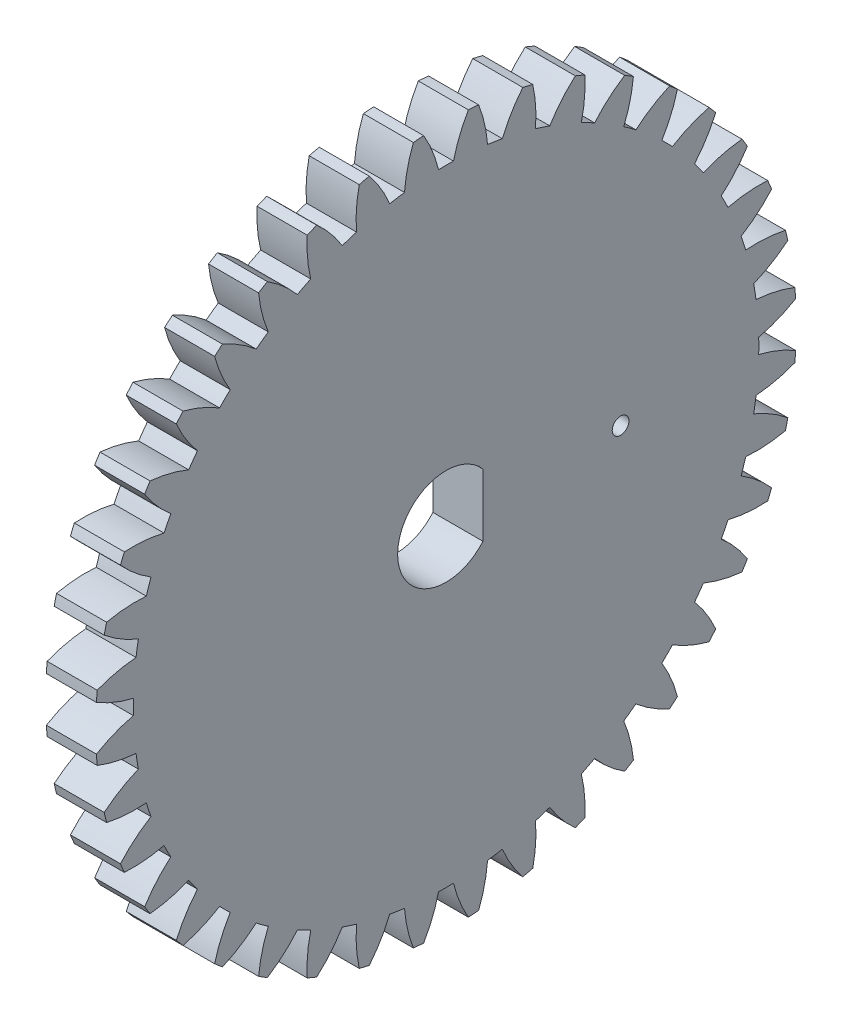
SolidWorks part; units mm, degrees
ref_plane "Plane1" through (0, 0, 0) normal (0, 0, 1) x (1, 0, 0)
ref_plane "Plane2" through (0, 0, 0) normal (0, 1, 0) x (1, 0, 0)
ref_plane "Plane3" through (0, 0, 0) normal (1, 0, 0) x (0, 0, -1)
sketch "HoldingSke" plane through (0, 0, 0) normal (0, 1, 0) x (1, 0, 0)
  line L0 (0, 0) -> (0.766, -0.6428)
  line L1 (-15, 0) -> (100, 0) construction
  line L2 (0, 0) -> (-2.1039, 2.3779)
  line L3 (0, 0) -> (-11.863, 4.5341)
  line L4 (0, 0) -> (6.6156, 5.5511)
  line L5 (0, 0) -> (-46.8476, -17.4728)
  line L6 (0, 0) -> (-2.4869, -1.6779)
  line L7 (-2.1039, 2.3779) -> (8.6587, 51.2065)
  line L8 (-76.2, 54.61) -> (-75.2, 54.61)
  line L9 (-71.009, 38.7566) -> (-53.1078, 45.2721)
  line L10 (-76.2, 71.12) -> (104.1128, 71.12)
  line L11 (0, 0) -> (-3, 0)
  line L12 (-76.2, 101.6) -> (-76.162, 101.6)
  line L13 (24.9733, 27.94) -> (52.9518, 28.4284)
  line L14 (24.9733, 27.94) -> (24.9743, 27.94)
  line L15 (24.9733, 27.94) -> (100.4006, 29.5858)
  line L16 (-63.627, -1) -> (-12.827, -1)
  circle A0 centre (0, 0) radius 3
  circle A1 centre (0, 0) radius 18.749
  circle A2 centre (0, 0) radius 37.5
  circle A3 centre (0, 0) radius 3
  dimension "MHD" = 37.498
  dimension "Hub_dia" = 75
  dimension "Bore" = 6
  dimension "MBD" = 6
  dimension "Num_teeth" = 40
  dimension "Pitch" = 1
  dimension "Overall_len" = 50
  dimension "Show_teeth" = 40
  dimension "Thickness" = 3
  dimension "OAL" = 50.0007
  dimension "T_dim" = 1
  dimension "Ap" = 20
  dimension "H" = 19.05
  dimension "Pitch_radius" = 180.3128
  dimension "Width" = 3
  dimension "Backlash" = 0.038
  dimension "Addendum_fac" = 1
  dimension "Dedendum_fac" = 1.25
  dimension "Clearance_fac" = 0.25
  dimension "Dedendum_add" = 0.001
  dimension "Module" = 1
sketch "BasProSke" plane through (0, 0, 0) normal (0, 1, 0) x (1, 0, 0)
  line L0 (-10, 0) -> (60, 0) construction
  line L1 (0, 0) -> (0, 21)
  line L2 (0, 0) -> (3, 0)
  line L3 (3, 0) -> (3, 21)
  line L4 (3, 21) -> (0, 21)
  dimension "Thickness" = 3
  dimension "Diameter" = 42
revolve "Base-Revolve" add sketch "BasProSke" angle 360 about L0
sketch "TooCutSke" plane through (0, 0, 0) normal (1, 0, 0) x (0, 0, -1)
  line L1 (0, 0) -> (0, 107) construction
  line L2 (0, 0) -> (-0.8517, 19.9819) construction
  line L3 (0, 0) -> (-3.1363, 39.8509) construction
  line L4 (-0.8517, 19.9819) -> (-1.5682, 19.9255) construction
  arc A0 (0.4487, 18.7436) -> (-0.4487, 18.7436) centre (0, 0) ccw
  arc A1 (1.3547, 20.9817) -> (-1.3547, 20.9817) centre (0, 0) ccw
  circle A2 centre (0, 0) radius 20 construction
  circle A3 centre (0, 0) radius 18.7939 construction
  arc A4 (-0.4487, 18.7436) -> (-1.3547, 20.9817) centre (-8.2322, 16.895) ccw
  arc A5 (1.3547, 20.9817) -> (0.4487, 18.7436) centre (8.2322, 16.895) ccw
  dimension "Root_dia" = 37.498
  dimension "Overcut_dia" = 42.0508
  dimension "Pitch_dia" = 40
  dimension "Base_dia" = 37.5877
  dimension "Flank_rad" = 8
  dimension "Half_ang" = 4.5
  dimension "Half_CT" = 0.7187
extrude "ToothCut" cut sketch "TooCutSke" along normal through all
fillet "Breaks" [suppressed] radius 0.02
fillet "RootFillets" [suppressed] radius 0.251
pattern_circular "TeethCuts" count 40 every 9 about axis through (-10, 0, 0) along (1, 0, 0) of "ToothCut", "RootFillets", "Breaks"
sketch "HubNeaOneSke" plane through (0, 0, 0) normal (-1, 0, 0) x (0, 0, 1)
  circle A0 centre (0, 0) radius 18.749
  dimension "Diameter" = 37.498
extrude "HubNearOne" [suppressed] add sketch "HubNeaOneSke" along normal blind 47.0007
sketch "HubNeaBotSke" plane through (0, 0, 0) normal (-1, 0, 0) x (0, 0, 1)
  circle A0 centre (0, 0) radius 18.749
  dimension "Diameter" = 37.498
extrude "HubNearBoth" [suppressed] add sketch "HubNeaBotSke" along normal blind 23.5004
ref_plane "FarPln" through (3, 0, 0) normal (1, 0, 0) x (0, 0, -1)
sketch "HubFarSke" plane through (3, 0, 0) normal (1, 0, 0) x (0, 0, -1)
  circle A0 centre (0, 0) radius 18.749
  dimension "Diameter" = 37.498
extrude "HubFar" [suppressed] add sketch "HubFarSke" along normal blind 23.5004
sketch "BorSke" plane through (0, 0, 0) normal (1, 0, 0) x (0, 0, -1)
  circle A0 centre (0, 0) radius 1.5
  dimension "Diameter" = 3
extrude "Bore" cut sketch "BorSke" along normal mid plane 100.0014
sketch "KeySke" plane through (0, 0, 0) normal (1, 0, 0) x (0, 0, -1)
  line L0 (-1, 0) -> (-1, 4)
  line L1 (-1, 4) -> (1, 4)
  line L2 (1, 4) -> (1, 0)
  line L3 (0, 0) -> (0, 34) construction
  line L4 (-1, 0) -> (1, 0)
  dimension "Offset" = 4
  dimension "Width" = 2
extrude "Keyway" [suppressed] cut sketch "KeySke" along normal mid plane 100.0014
pattern_circular "Keyway2" [suppressed] count 2 every 90 about axis through (-10, 0, 0) along (1, 0, 0)
sketch "Sketch1" plane through (3, 0, 0) normal (1, 0, 0) x (0, 0, -1)
  line L0 (2.2123, -1.875) -> (2.2123, 1.875)
  arc A0 (2.2123, 1.875) -> (2.2123, -1.875) centre (0, 0) ccw
  circle A1 centre (10.4632, 0) radius 0.5
  dimension "D1" = 3.75
  dimension "D2" = 5.8
  dimension "D3" = 1
extrude "Cut-Extrude1" cut sketch "Sketch1" against normal through all
equation "' \"Module@HoldingSke\" = 6.35"
equation "' \"Num_teeth@HoldingSke\" = 12"
equation "' \"Ap@HoldingSke\" =  20"
equation "' \"Ap@HoldingSke\" = 20"
equation "' \"Width@HoldingSke\" = 0.5 * 25.4"
equation "' \"Hub_dia@HoldingSke\"= 1 * 25.4"
equation "' \"Hub_dia@HoldingSke\" = 1 * 25.4"
equation "' \"Overall_len@HoldingSke\" = 1.0 * 25.4"
equation "' \"T_dim@HoldingSke\" = 0.1 * 25.4"
equation "' \"Width@KeySke\" = 0.25 * 25.4"
equation "' \"Show_teeth@HoldingSke\" = 13"
equation "' \"Backlash@HoldingSke\" = 0.009 * 25.4"
equation "' \"Addendum_fac@HoldingSke\" = 1.0"
equation "' \"Dedendum_fac@HoldingSke\" = 1.25"
equation "' \"Dedendum_add@HoldingSke\" = 0.00005 * 25.4"
equation "' \"Clearance_fac@HoldingSke\" = 0.25"
equation "\"Pitch@HoldingSke\" = 1 / \"Module@HoldingSke\""
equation "\"Overcut_dia@TooCutSke\" = (\"Num_teeth@HoldingSke\" + 2 * \"Addendum_fac@HoldingSke\") / \"Pitch@HoldingSke\" + 0.002 * 25.4"
equation "\"Pitch_dia@TooCutSke\" = \"Num_teeth@HoldingSke\" / \"Pitch@HoldingSke\""
equation "\"Base_dia@TooCutSke\" = \"Num_teeth@HoldingSke\" / \"Pitch@HoldingSke\" * cos((\"Ap@HoldingSke\"  * 3.14159265 / 180))"
equation "\"Root_dia@TooCutSke\" = (\"Num_teeth@HoldingSke\" + 2) / \"Pitch@HoldingSke\" - 2 * (\"Addendum_fac@HoldingSke\" + \"Dedendum_fac@HoldingSke\") / \"Pitch@HoldingSke\" - \"Dedendum_add@HoldingSke\" * 2"
equation "\"Half_ang@TooCutSke\" = 180 / \"Num_teeth@HoldingSke\""
equation "\"Half_CT@TooCutSke\" = \"Num_teeth@HoldingSke\" / \"Pitch@HoldingSke\" * sin((3.14159265 / 2 / \"Num_teeth@HoldingSke\")) / 2 - 7 * \"Backlash@HoldingSke\" / 4"
equation "\"Flank_rad@TooCutSke\" = \"Num_teeth@HoldingSke\" / \"Pitch@HoldingSke\" / 5"
equation "\"Radius@RootFillets\" = \"Clearance_fac@HoldingSke\" / \"Pitch@HoldingSke\" + \"Dedendum_add@HoldingSke\""
equation "\"Break_rad@Breaks\" = 0.02 / \"Pitch@HoldingSke\""
equation "\"Thickness@HoldingSke\" = \"Width@HoldingSke\""
equation "\"OAL@HoldingSke\" = \"Thickness@HoldingSke\""
equation "\"MHD@HoldingSke\" = (\"Num_teeth@HoldingSke\" + 2) / \"Pitch@HoldingSke\" - 2 * (\"Addendum_fac@HoldingSke\" + \"Dedendum_fac@HoldingSke\")  / \"Pitch@HoldingSke\" - \"Dedendum_add@HoldingSke\" * 2"
equation "\"MBD@HoldingSke\" = (\"Num_teeth@HoldingSke\" + 2) / \"Pitch@HoldingSke\" - 2 * (\"Addendum_fac@HoldingSke\" + \"Dedendum_fac@HoldingSke\")  / \"Pitch@HoldingSke\" - \"Dedendum_add@HoldingSke\" * 2 - 0.002 * 25.4"
equation "\"MHD@HoldingSke\" = ((sgn( \"MHD@HoldingSke\" - \"Hub_dia@HoldingSke\" )-1)*( \"MHD@HoldingSke\" - \"Hub_dia@HoldingSke\" ))/-2+ \"Hub_dia@HoldingSke\""
equation "\"MBD@HoldingSke\" = ((sgn( \"MBD@HoldingSke\" - \"Bore@HoldingSke\" )-1)*( \"MBD@HoldingSke\" - \"Bore@HoldingSke\" ))/-2+ \"Bore@HoldingSke\""
equation "\"OAL@HoldingSke\" = ((sgn( \"OAL@HoldingSke\" - \"Overall_len@HoldingSke\" )+1)*( \"OAL@HoldingSke\" - \"Overall_len@HoldingSke\" ))/2 + \"Overall_len@HoldingSke\" + 0.000002 * 25.4"
equation "\"Num_teeth@TeethCuts\" = int( \"Show_teeth@HoldingSke\" ) + 1"
equation "\"Num_teeth@TeethCuts\" = ((sgn( \"Num_teeth@TeethCuts\" - \"Num_teeth@HoldingSke\" )-1)*( \"Num_teeth@TeethCuts\" - \"Num_teeth@HoldingSke\" ))/-2+ \"Num_teeth@HoldingSke\""
equation "\"Num_teeth@TeethCuts\" = ((sgn( \"Num_teeth@TeethCuts\" - 2.0)+1)*( \"Num_teeth@TeethCuts\" - 2.0))/2 +2.0"
equation "\"Angle@TeethCuts\" = 360.0 / \"Num_teeth@HoldingSke\""
equation "\"Diameter@BasProSke\" = (\"Num_teeth@HoldingSke\" + 2 * \"Addendum_fac@HoldingSke\") / \"Pitch@HoldingSke\""
equation "\"Thickness@BasProSke\"  = \"Thickness@HoldingSke\""
equation "' \"Fillet_rad@BasProSke\" =  \"Thickness@HoldingSke\" * 0.05"
equation "' \"Fillet_rad@BasProSke\" = \"Thickness@HoldingSke\" * 0.05"
equation "\"MHD@HoldingSke\" = ((sgn( \"MHD@HoldingSke\" - \"Root_dia@TooCutSke\" )-1)*( \"MHD@HoldingSke\" - \"Root_dia@TooCutSke\" ))/-2+ \"Root_dia@TooCutSke\""
equation "\"Diameter@HubNeaOneSke\" = \"MHD@HoldingSke\""
equation "\"Length@HubNearOne\" = \"OAL@HoldingSke\" - \"Thickness@BasProSke\""
equation "\"Diameter@HubNeaBotSke\" = \"MHD@HoldingSke\""
equation "\"Length@HubNearBoth\" = ( \"OAL@HoldingSke\" - \"Thickness@BasProSke\" ) / 2.0"
equation "\"Thickness@FarPln\" = \"Thickness@BasProSke\""
equation "\"Diameter@HubFarSke\" = \"MHD@HoldingSke\""
equation "\"Length@HubFar\" = ( \"OAL@HoldingSke\" - \"Thickness@BasProSke\" ) / 2.0"
equation "\"D1@Bore\" = \"OAL@HoldingSke\" * 2.0"
equation "\"D1@Keyway\" = \"OAL@HoldingSke\" * 2.0"
equation "\"Offset@KeySke\" = \"T_dim@HoldingSke\" + \"MBD@HoldingSke\" / 2.0"
